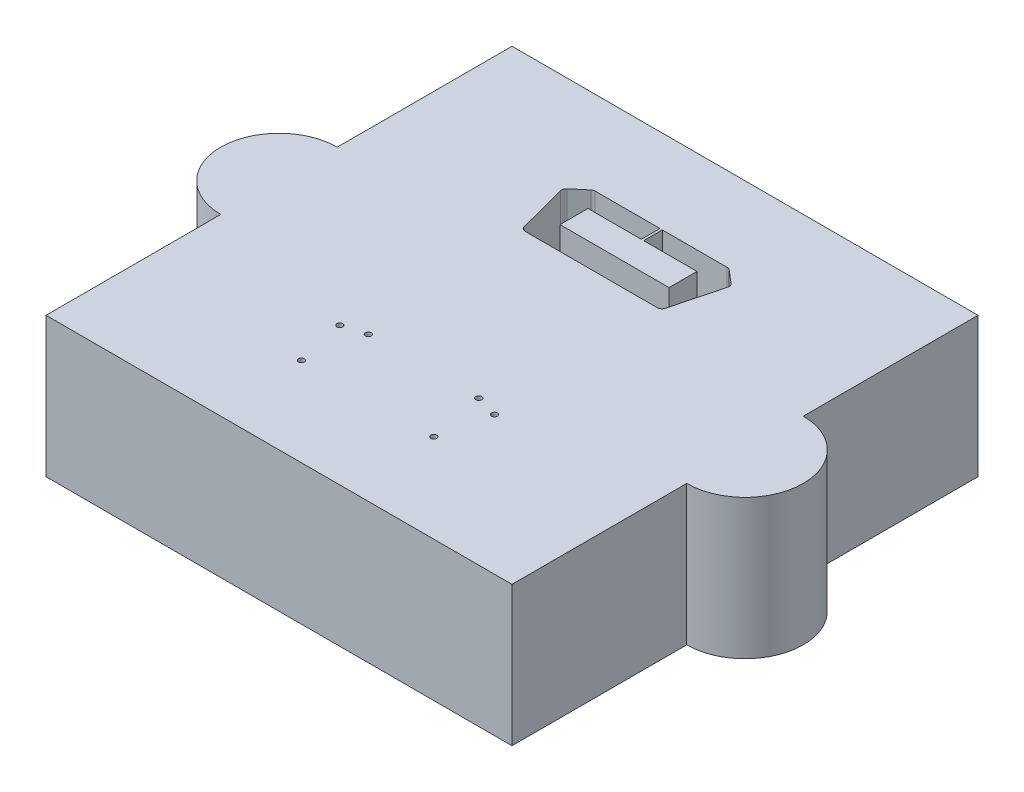
SolidWorks part; units mm, degrees
ref_plane "Front Plane" through (0, 0, 0) normal (0, 0, 1) x (1, 0, 0)
ref_plane "Top Plane" through (0, 0, 0) normal (0, 1, 0) x (1, 0, 0)
ref_plane "Right Plane" through (0, 0, 0) normal (1, 0, 0) x (0, 0, -1)
sketch "Sketch2" plane through (0, 0, 0) normal (0, 1, 0) x (1, 0, 0)
  line L0 (0, 0) -> (0, -69020.5892) construction
  line L1 (0, 0) -> (69020.5892, 0) construction
  line L5 (-50, -75) -> (50, -75)
  line L8 (-50, 25) -> (50, 25)
  line L9 (50, 25) -> (50, -12.5)
  line L10 (-50, 25) -> (-50, -12.5)
  line L11 (-50, -37.5) -> (-50, -75)
  line L12 (50, -37.5) -> (50, -75)
  arc A2 (-50, -12.5) -> (-50, -37.5) centre (-50, -25) ccw
  arc A3 (50, -37.5) -> (50, -12.5) centre (50, -25) ccw
  dimension "D3" = 25
  dimension "D4" = 25
  dimension "D7" = 50
  dimension "D5" = 25
  dimension "D1" = 100
  dimension "D2" = 25
  dimension "D6" = 75
extrude "Boss-Extrude1" add sketch "Sketch2" against normal blind 30
sketch "Sketch1" plane through (0, 0, 0) normal (0, 1, 0) x (1, 0, 0)
  line L0 (0, 0) -> (0, -45253.2958) construction
  line L1 (0, 0) -> (45253.2958, 0) construction
  line L34 (-14.1786, -8) -> (14.1786, -8)
  line L39 (-11.7, 3) -> (-0.25, 3)
  line L40 (-11.7, 3) -> (-11.7, -3)
  line L41 (-11.7, -3) -> (11.7, -3)
  line L42 (11.7, 3) -> (11.7, -3)
  line L43 (-14.1841, 7) -> (-0.25, 7)
  line L44 (-15.1459, -7.2539) -> (-17.9398, 3.3896)
  line L45 (-17.618, 4.4073) -> (-14.8295, 6.7638)
  line L46 (15.1459, -7.2539) -> (17.9398, 3.3896)
  line L47 (17.618, 4.4073) -> (14.8295, 6.7638)
  line L48 (-0.25, 7) -> (-0.25, 3)
  line L49 (0.25, 7) -> (0.25, 3)
  line L50 (0.25, 7) -> (14.1841, 7)
  line L51 (0.25, 3) -> (11.7, 3)
  arc A18 (-14.1786, -8) -> (-15.1459, -7.2539) centre (-14.1786, -7) cw
  arc A19 (-17.9398, 3.3896) -> (-17.618, 4.4073) centre (-16.9725, 3.6435) cw
  arc A20 (-14.8295, 6.7638) -> (-14.1841, 7) centre (-14.1841, 6) cw
  arc A21 (14.1841, 7) -> (14.8295, 6.7638) centre (14.1841, 6) cw
  arc A22 (17.618, 4.4073) -> (17.9398, 3.3896) centre (16.9725, 3.6435) cw
  arc A23 (14.1786, -8) -> (15.1459, -7.2539) centre (14.1786, -7) ccw
  point P43 (0, 0)
  point P44 (0, 0)
  dimension "D4" = 1
  dimension "D5" = 1
  dimension "D6" = 1
  dimension "D7" = 1
  dimension "D8" = 1
  dimension "D9" = 1
  dimension "D10" = 28.3681
  dimension "D11" = 28.3572
  dimension "D15" = 10.6435
  dimension "D16" = 10.6435
  dimension "D19" = 3.7557
  dimension "D1" = 6
  dimension "D2" = 5
  dimension "D3" = 4
  dimension "D12" = 33.9451
  dimension "D13" = 13.9341
  dimension "D14" = 11.45
  dimension "D17" = 2.7939
  dimension "D18" = 2.7939
  dimension "D21" = 0.5
  dimension "D24" = 23.4
extrude "Cut-Extrude2" cut sketch "Sketch1" against normal blind 20
sketch "Sketch3" plane through (0, 0, 0) normal (0, 1, 0) x (1, 0, 0)
  line L0 (0, 0) -> (0, -50000) construction
  line L1 (11.6875, -2.85) -> (-11.6875, -2.85) construction
  line L2 (0, -50) -> (50000, -50) construction
  circle A12 centre (-14.2175, -55.9615) radius 0.625
  circle A13 centre (14.1825, -55.9615) radius 0.625
  circle A14 centre (-16.6175, -45.318) radius 0.625
  circle A15 centre (16.5825, -45.318) radius 0.625
  circle A16 centre (-11.8675, -43.9615) radius 0.625
  circle A17 centre (11.8325, -43.9615) radius 0.625
  point P5 (0, -2.85)
  point P8 (0, 0)
  point P21 (0, 0)
  point P22 (0, 0)
  point P23 (15.1282, -54.806)
  point P46 (0, 0)
  point P47 (0, 0)
  point P48 (0, 0)
  point P49 (0, 0)
  dimension "D4" = 4.75
  dimension "D10" = 2.4
  dimension "D7" = 10.6435
  dimension "D9" = 23.7
  dimension "D12" = 1.25
  dimension "D1" = 50
  dimension "D2" = 28.4
  dimension "D3" = 4.75
  dimension "D5" = 1.3565
  dimension "D6" = 1.3565
  dimension "D8" = 10.6435
  dimension "D11" = 2.4
  dimension "D13" = 6.0385
  dimension "D14" = 11.8325
extrude "Cut-Extrude3" cut sketch "Sketch3" against normal blind 10
sketch "Sketch4" plane through (0, -30, 0) normal (0, -1, 0) x (1, 0, 0)
  line L0 (0, 0) -> (0, -50000) construction
  line L1 (0, 0) -> (50000, 0) construction
  line L3 (-30, 15) -> (30, 15)
  line L4 (-30, 15) -> (-30, -15)
  line L5 (-30, -15) -> (30, -15)
  line L6 (30, 15) -> (30, -15)
  line L7 (-30, 15) -> (30, -15) construction
  line L8 (-30, -15) -> (30, 15) construction
  point P5 (0, 0)
  dimension "D1" = 60
  dimension "D2" = 30
extrude "Cut-Extrude4" cut sketch "Sketch4" against normal blind 10
sketch "Sketch5" plane through (0, -30, 0) normal (0, -1, 0) x (1, 0, 0)
  line L0 (0, 49991.2144) -> (0, -50000) construction
  line L1 (0.1, -7.15) -> (0.1, -2.85) construction
  line L7 (50, -25) -> (-50, -25) construction
  line L8 (-30, 65) -> (30, 65)
  line L9 (-30, 65) -> (-30, 35)
  line L10 (-30, 35) -> (30, 35)
  line L11 (30, 65) -> (30, 35)
  line L12 (-30, 65) -> (30, 35) construction
  line L13 (-30, 35) -> (30, 65) construction
  point P5 (0.1, -5)
  point P7 (0, 50)
  dimension "D1" = 75
  dimension "D2" = 30
  dimension "D3" = 60
extrude "Cut-Extrude5" cut sketch "Sketch5" against normal blind 20
sketch "Sketch7" plane through (0, 0, 0) normal (0, 1, 0) x (1, 0, 0)
  circle A0 centre (-50, -25) radius 2.5
  circle A1 centre (50, -25) radius 2.5
  dimension "D1" = 5
